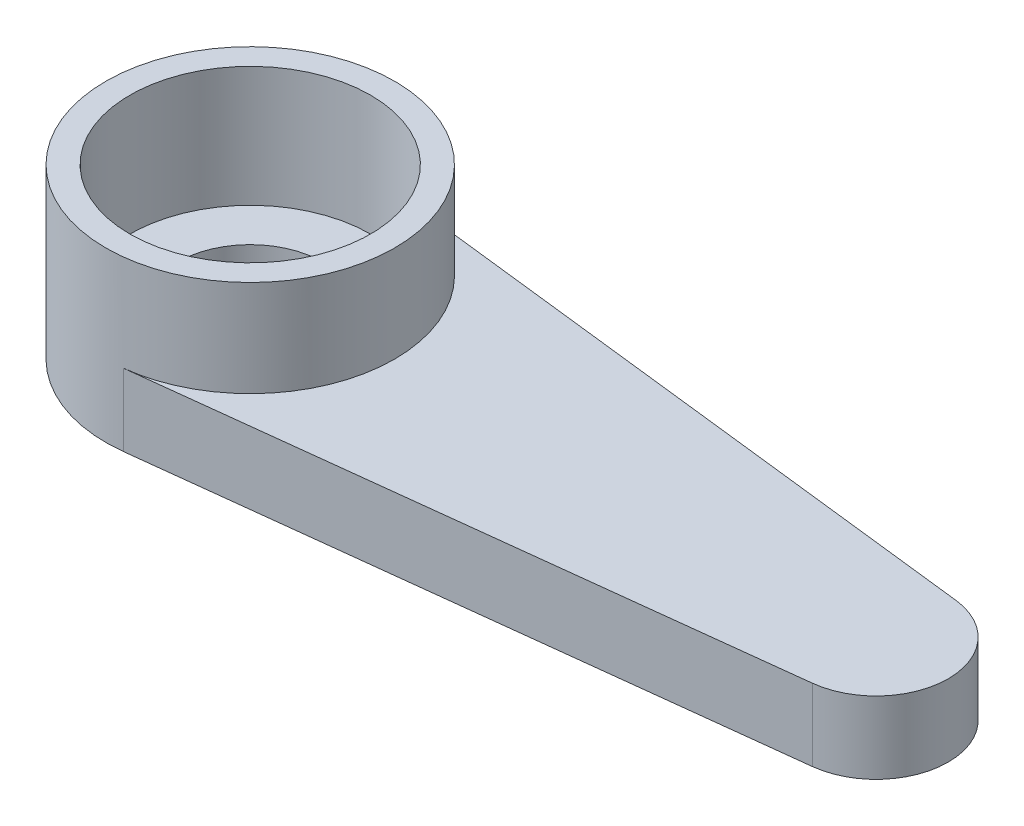
SolidWorks part; units mm, degrees
material "Nylon 101"
ref_plane "Front Plane" through (0, 0, 0) normal (0, 0, 1) x (1, 0, 0)
ref_plane "Top Plane" through (0, 0, 0) normal (0, 1, 0) x (1, 0, 0)
ref_plane "Right Plane" through (0, 0, 0) normal (1, 0, 0) x (0, 0, -1)
sketch "Sketch1" plane through (0, 0, 0) normal (0, 1, 0) x (1, 0, 0)
  line L0 (0.3462, 2.98) -> (13.1731, 1.49)
  line L3 (13.1731, -1.49) -> (0.3462, -2.98)
  arc A0 (0.3462, 2.98) -> (0.3462, -2.98) centre (0, 0) ccw
  arc A1 (13.1731, -1.49) -> (13.1731, 1.49) centre (13, 0) ccw
  circle A2 centre (0, 0) radius 1.5
  dimension "D2" = 3
  dimension "D3" = 6
  dimension "D4" = 3
  dimension "D1" = 13
extrude "Boss-Extrude1" add sketch "Sketch1" along normal blind 1.5
sketch "Sketch2" plane through (0, 1.5, 0) normal (0, 1, 0) x (1, 0, 0)
  line L0 (13.1731, 1.49) -> (0.3462, 2.98) construction
  circle A0 centre (0, 0) radius 3
  circle A1 centre (0, 0) radius 2.5
  dimension "D1" = 5
extrude "Boss-Extrude2" add sketch "Sketch2" along normal blind 2
sketch "Sketch3" plane through (0, 1.5, 0) normal (0, 1, 0) x (1, 0, 0)
  circle A0 centre (0, 0) radius 2.5
extrude "Cut-Extrude1" cut sketch "Sketch3" against normal blind 0.5
